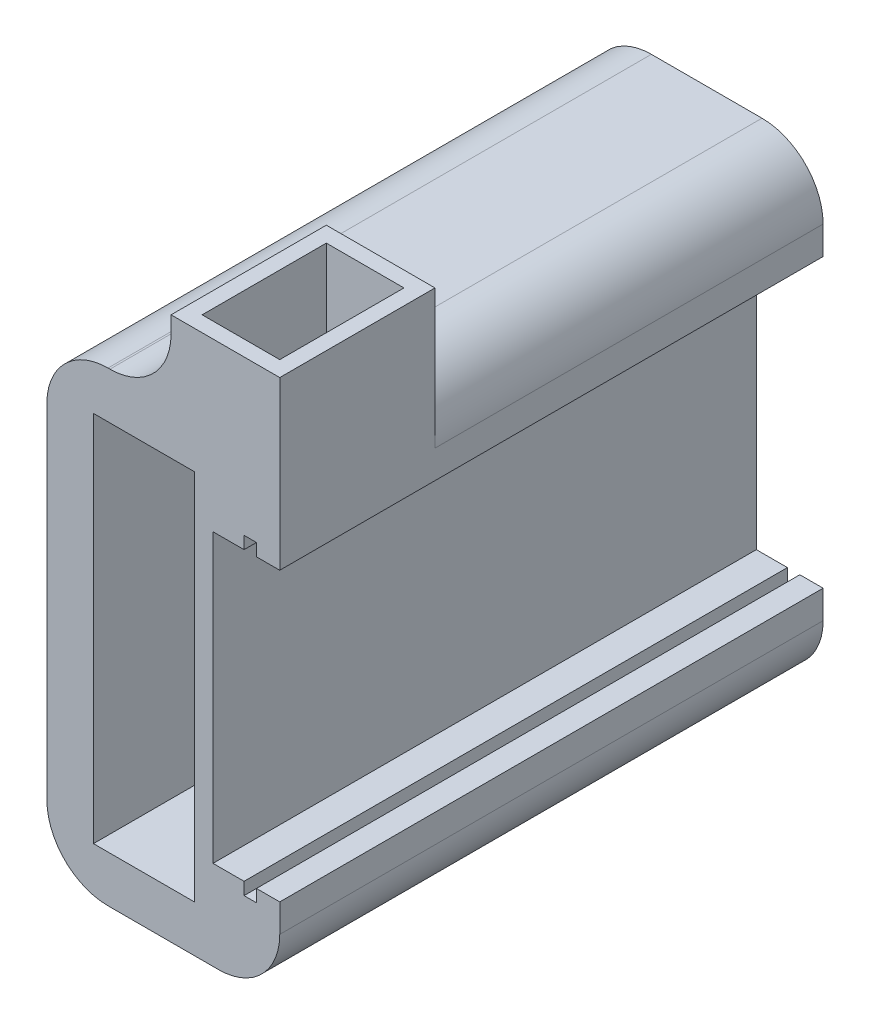
SolidWorks part; units mm, degrees
ref_plane "Front Plane" through (0, 0, 0) normal (0, 0, 1) x (1, 0, 0)
ref_plane "Top Plane" through (0, 0, 0) normal (0, 1, 0) x (1, 0, 0)
ref_plane "Right Plane" through (0, 0, 0) normal (1, 0, 0) x (0, 0, -1)
sketch "Sketch1" plane through (0, 0, 0) normal (0, 1, 0) x (1, 0, 0)
  line L1 (0, 0) -> (38.1, 0)
  line L2 (0, 0) -> (0, 88.9)
  line L3 (0, 88.9) -> (38.1, 88.9)
  line L4 (38.1, 0) -> (38.1, 88.9)
  dimension "D1" = 88.9
  dimension "D2" = 38.1
extrude "Boss-Extrude1" add sketch "Sketch1" along normal blind 76.2
sketch "Sketch2" plane through (0, 0, 0) normal (0, 0, 1) x (1, 0, 0)
  line L0 (0, 76.2) -> (0, 0) construction
  line L1 (7.62, 68.58) -> (24.13, 68.58)
  line L2 (7.62, 68.58) -> (7.62, 7.62)
  line L3 (7.62, 7.62) -> (24.13, 7.62)
  line L4 (24.13, 68.58) -> (24.13, 7.62)
  line L5 (0, 76.2) -> (38.1, 76.2) construction
  line L6 (0, 0) -> (38.1, 0) construction
  dimension "D1" = 7.62
  dimension "D2" = 7.62
  dimension "D3" = 7.62
  dimension "D4" = 16.51
extrude "Cut-Extrude1" cut sketch "Sketch2" against normal blind 76.2
sketch "Sketch3" plane through (0, 0, 0) normal (0, 0, 1) x (1, 0, 0)
  line L0 (38.1, 61.595) -> (24.13, 61.595)
  line L1 (34.29, 63.627) -> (32.258, 63.627)
  line L2 (34.29, 63.627) -> (34.29, 12.573)
  line L3 (34.29, 12.573) -> (32.258, 12.573)
  line L4 (32.258, 63.627) -> (32.258, 12.573)
  line L5 (38.1, 76.2) -> (38.1, 0) construction
  line L6 (24.13, 7.62) -> (24.13, 68.58) construction
  line L7 (38.1, 14.605) -> (24.13, 14.605)
  line L8 (24.13, 7.62) -> (24.13, 68.58) construction
  line L9 (27.178, 61.595) -> (27.178, 14.605)
  point P12 (32.258, 38.1)
  point P13 (24.13, 38.1)
  line M13 (38.1, 0) -> (38.1, 76.2)
  dimension "D1" = 51.054
  dimension "D2" = 2.032
  dimension "D3" = 2.032
  dimension "D4" = 2.032
  dimension "D5" = 3.81
  dimension "D6" = 5.08
extrude "Cut-Extrude2" cut sketch "Sketch3" against normal through all contours L0 L9 L7 L4 | L7 L2 L0 L4 | L7 L0 L2 M13 | L1 L4 L0 L2 | L2 L7 L4 L3
sketch "Sketch5" plane through (0, 76.2, 0) normal (0, 1, 0) x (1, 0, 0)
  line L3 (38.1, 0) -> (38.1, 88.9) construction
  line L4 (33.02, 2.54) -> (25.4, 2.54)
  line L5 (33.02, 2.54) -> (33.02, 15.24)
  line L6 (33.02, 15.24) -> (25.4, 15.24)
  line L7 (25.4, 2.54) -> (25.4, 15.24)
  line L8 (0, 0) -> (38.1, 0) construction
  dimension "D1" = 5.08
  dimension "D2" = 2.54
  dimension "D3" = 12.7
  dimension "D4" = 7.62
extrude "Cut-Extrude3" cut sketch "Sketch5" against normal up to surface (14.605 mm away) up to face at (29.718, 61.595, -44.45)
sketch "Sketch6" plane through (0, 76.2, 0) normal (0, 1, 0) x (1, 0, 0)
  line L0 (38.1, 0) -> (38.1, 88.9) construction
  line L1 (38.1, 0) -> (20.32, 0)
  line L2 (38.1, 0) -> (38.1, 25.4)
  line L3 (38.1, 25.4) -> (20.32, 25.4)
  line L4 (20.32, 0) -> (20.32, 25.4)
  line L5 (0, 0) -> (38.1, 0) construction
  line L7 (22.86, 22.86) -> (35.56, 22.86)
  line L8 (22.86, 22.86) -> (22.86, 2.54)
  line L9 (22.86, 2.54) -> (35.56, 2.54)
  line L10 (35.56, 22.86) -> (35.56, 2.54)
  dimension "D1" = 17.78
  dimension "D2" = 25.4
  dimension "D3" = 2.54
  dimension "D4" = 2.54
  dimension "D5" = 2.54
  dimension "D6" = 2.54
extrude "Boss-Extrude2" add sketch "Sketch6" along normal blind 12.7
fillet "Fillet2" radius 10 5 edges at (38.1, 76.2, -57.15) (20.32, 76.2, -12.7) (0, 76.2, -44.45) (0, 0, -44.45) (38.1, 0, -44.45)
sketch "Sketch7" plane through (0, 0, -88.9) normal (0, 0, -1) x (-1, 0, 0)
  line L0 (-27.178, 61.595) -> (0, 61.595) construction
  line L1 (0, 66.2) -> (0, 10) construction
  line L2 (-13.589, 63.5) -> (-13.589, 12.7) construction
  circle A0 centre (-13.589, 63.5) radius 2.7305
  circle A1 centre (-13.589, 12.7) radius 2.7305
  point P4 (-13.589, 61.595)
  point P5 (0, 38.1)
  point P6 (-13.589, 38.1)
  dimension "D1" = 5.461
  dimension "D2" = 5.461
  dimension "D3" = 50.8
extrude "Cut-Extrude4" cut sketch "Sketch7" against normal up to surface (12.7 mm away) up to face at (15.875, 38.1, -76.2)
